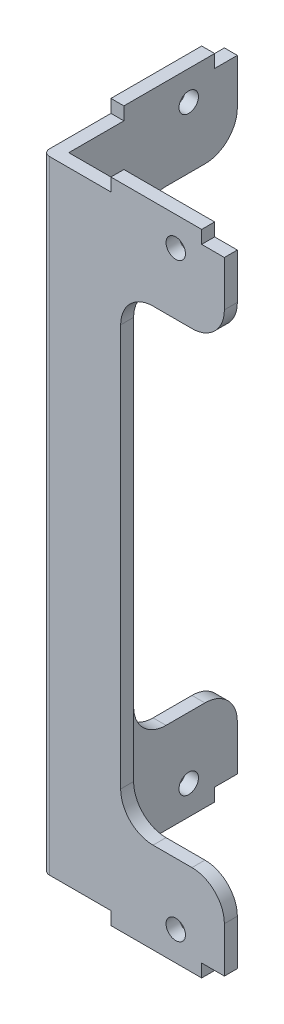
SolidWorks part; units mm, degrees
material "6061-T4 (SS)"
ref_plane "Front Plane" through (0, 0, 0) normal (0, 0, 1) x (1, 0, 0)
ref_plane "Top Plane" through (0, 0, 0) normal (0, 1, 0) x (1, 0, 0)
ref_plane "Right Plane" through (0, 0, 0) normal (1, 0, 0) x (0, 0, -1)
sketch "Sketch1" plane through (0, 0, 0) normal (0, 0, 1) x (1, 0, 0)
  line L0 (0, 96) -> (0, 0)
  line L1 (0, 0) -> (10.5, 0)
  line L2 (28, 0) -> (28, 7)
  line L3 (23, 12) -> (17, 12)
  line L4 (12, 17) -> (12, 79)
  line L5 (17, 84) -> (23, 84)
  line L6 (28, 89) -> (28, 96)
  line L7 (28, 96) -> (24.5, 96)
  line L8 (10.5, 96) -> (10.5, 98)
  line L9 (10.5, 98) -> (24.5, 98)
  line L10 (24.5, 98) -> (24.5, 96)
  line L11 (10.5, 96) -> (0, 96)
  line L12 (10.5, 0) -> (10.5, -2)
  line L13 (10.5, -2) -> (24.5, -2)
  line L14 (24.5, -2) -> (24.5, 0)
  line L15 (24.5, 0) -> (28, 0)
  arc A0 (28, 89) -> (23, 84) centre (23, 89) cw
  arc A1 (28, 7) -> (23, 12) centre (23, 7) ccw
  arc A2 (17, 12) -> (12, 17) centre (17, 17) cw
  arc A3 (17, 84) -> (12, 79) centre (17, 79) ccw
  circle A4 centre (20.5, 2.5) radius 1.5
  circle A5 centre (20.5, 93.5) radius 1.5
  dimension "D2" = 5
  dimension "D12" = 3
  dimension "D1" = 96
  dimension "D3" = 12
  dimension "D4" = 2
  dimension "D5" = 14
  dimension "D6" = 2
  dimension "D7" = 28
  dimension "D8" = 12
  dimension "D9" = 10.5
  dimension "D10" = 20.5
  dimension "D11" = 2.5
  dimension "D13" = 2.5
extrude "Boss-Extrude1" add sketch "Sketch1" along normal blind 2
sketch "Sketch2" plane through (0, 0, 0) normal (-1, 0, 0) x (0, 0, 1)
  line L0 (0, 96) -> (-8.5, 96)
  line L1 (-8.5, 96) -> (-8.5, 98)
  line L2 (-8.5, 98) -> (-22.5, 98)
  line L3 (-22.5, 98) -> (-22.5, 96)
  line L4 (-22.5, 96) -> (-26, 96)
  line L5 (-26, 96) -> (-26, 89)
  line L6 (-21, 84) -> (-15, 84)
  line L7 (-10, 79) -> (-10, 17)
  line L8 (-15, 12) -> (-21, 12)
  line L9 (-26, 7) -> (-26, 0)
  line L10 (-26, 0) -> (-22.5, 0)
  line L11 (-22.5, 0) -> (-22.5, -2)
  line L12 (-22.5, -2) -> (-8.5, -2)
  line L13 (-8.5, -2) -> (-8.5, 0)
  line L14 (-8.5, 0) -> (0, 0)
  line L15 (0, 96) -> (0, 0) construction
  line L16 (0, 0) -> (0, 96)
  line L17 (2, 98) -> (0, 98) construction
  line L18 (2, 96) -> (2, 0) construction
  line L19 (2, -2) -> (0, -2) construction
  arc A0 (-26, 7) -> (-21, 12) centre (-21, 7) cw
  arc A1 (-10, 17) -> (-15, 12) centre (-15, 17) cw
  arc A2 (-21, 84) -> (-26, 89) centre (-21, 89) cw
  arc A3 (-10, 79) -> (-15, 84) centre (-15, 79) ccw
  circle A4 centre (-18.5, 93.5) radius 1.5
  circle A5 centre (-18.5, 2.5) radius 1.5
  dimension "D7" = 5
  dimension "D10" = 3
  dimension "D1" = 10
  dimension "D2" = 12
  dimension "D3" = 10.5
  dimension "D4" = 14
  dimension "D5" = 28
  dimension "D6" = 12
  dimension "D8" = 20.5
  dimension "D9" = 2.5
  dimension "D11" = 2.5
extrude "Boss-Extrude2" add sketch "Sketch2" against normal blind 2 contours L2 L3 L4 L5 A2 L6 A3 L7 A1 L8 A0 L9 L10 L11 L12 L13 L14 L16 L0 L1 | A5 | A4
fillet "Fillet1" radius 1 1 edges at (0, 48, 2)
